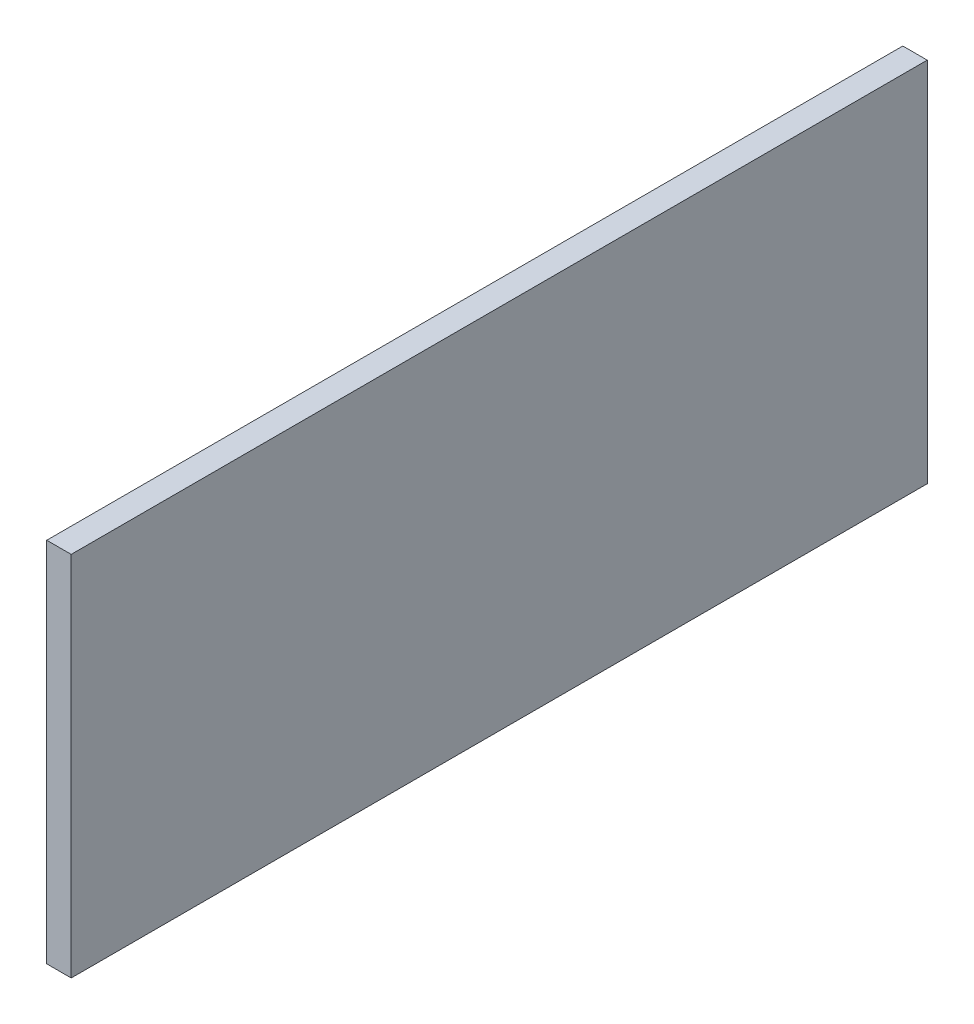
SolidWorks part; units mm, degrees
material "Aluminum Bronze"
ref_plane "Front Plane" through (0, 0, 0) normal (0, 0, 1) x (1, 0, 0)
ref_plane "Top Plane" through (0, 0, 0) normal (0, 1, 0) x (1, 0, 0)
ref_plane "Right Plane" through (0, 0, 0) normal (1, 0, 0) x (0, 0, -1)
sketch "Sketch2" plane through (0, 0, 0) normal (1, 0, 0) x (0, 0, -1)
  line L1 (-44.45, 19.05) -> (44.45, 19.05)
  line L2 (-44.45, 19.05) -> (-44.45, -19.05)
  line L3 (-44.45, -19.05) -> (44.45, -19.05)
  line L4 (44.45, 19.05) -> (44.45, -19.05)
  line L5 (0, -19.05) -> (0, 19.05) construction
  line L6 (-44.45, 0) -> (44.45, 0) construction
  point P0 (0, 0)
  dimension "D1" = 88.9
  dimension "D2" = 38.1
extrude "Boss-Extrude1" add sketch "Sketch2" along normal blind 2.54
sketch "Sketch3" plane through (0, 0, 0) normal (-1, 0, 0) x (0, 0, 1)
  text T0 "2025 CAD 190"
  text T1 "Part Modeling in Solidworks Champion" font "Century Gothic" height 3.5
